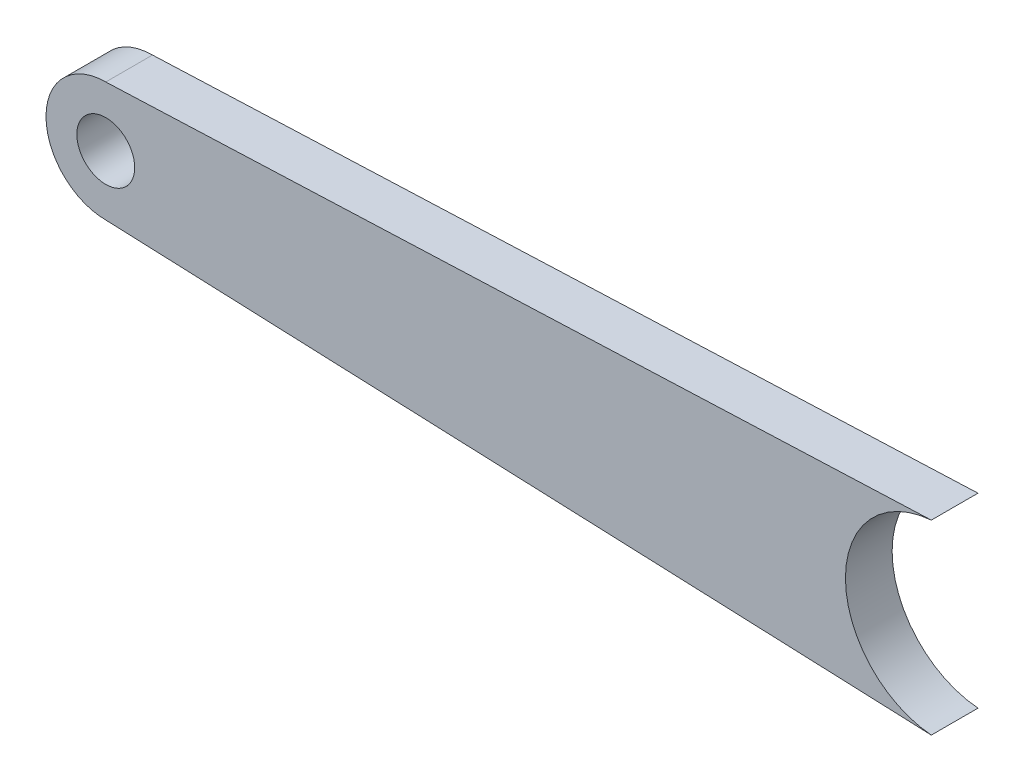
SolidWorks part; units mm, degrees
material "Cast Carbon Steel"
ref_plane "Front Plane" through (0, 0, 0) normal (0, 0, 1) x (1, 0, 0)
ref_plane "Top Plane" through (0, 0, 0) normal (0, 1, 0) x (1, 0, 0)
ref_plane "Right Plane" through (0, 0, 0) normal (1, 0, 0) x (0, 0, -1)
sketch "Sketch1" plane through (0, 0, 0) normal (0, 0, 1) x (1, 0, 0)
  circle A0 centre (0, 0) radius 3.937
  circle A1 centre (0, 0) radius 8.128
  dimension "D1" = 7.874
  dimension "D2" = 16.256
extrude "Boss-Extrude1" add sketch "Sketch1" along normal blind 6.35
sketch "Sketch2" plane through (0, 0, 6.35) normal (0, 0, 1) x (1, 0, 0)
  line L0 (0, 8.128) -> (113.284, 12.7)
  line L1 (0, -8.128) -> (113.284, -12.7)
  circle A0 centre (113.284, 0) radius 12.7
  circle A1 centre (0, 0) radius 8.128 construction
  arc A2 (113.284, 12.7) -> (113.284, -12.7) centre (113.284, 0) ccw
  arc A3 (0, 8.128) -> (0, -8.128) centre (0, 0) cw
  circle M1 centre (0, 0) radius 8.128
  dimension "D1" = 25.4
  dimension "D2" = 113.284
extrude "Boss-Extrude2" add sketch "Sketch2" against normal blind 6.35 contours A0 L0 L1 M1
